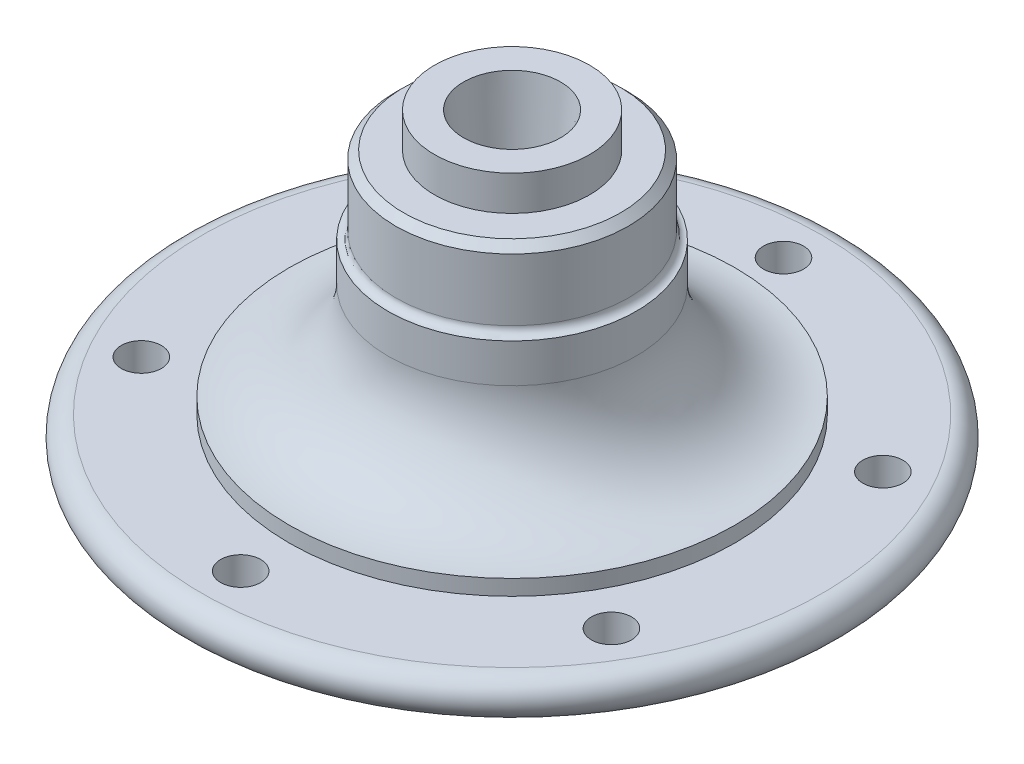
SolidWorks part; units mm, degrees
ref_plane "Front Plane" through (0, 0, 0) normal (0, 0, 1) x (1, 0, 0)
ref_plane "Top Plane" through (0, 0, 0) normal (0, 1, 0) x (1, 0, 0)
ref_plane "Right Plane" through (0, 0, 0) normal (1, 0, 0) x (0, 0, -1)
sketch "Croquis1" plane through (0, 0, 0) normal (0, 0, 1) x (1, 0, 0)
  line L0 (0, 0) -> (0, 90)
  line L1 (0, 90) -> (20, 90)
  line L2 (20, 90) -> (20, 81)
  line L3 (20, 81) -> (28, 81)
  line L4 (30, 79) -> (30, 62.995)
  line L5 (0, 0) -> (40, 0)
  line L6 (40, 0) -> (40, 12)
  line L7 (40, 12) -> (80, 12)
  line L9 (80, 22) -> (57.5, 22)
  line L10 (57.5, 22) -> (57.5, 26)
  line L11 (32, 60.995) -> (32, 50.995)
  line L12 (28, 81) -> (30, 79)
  arc A0 (80, 12) -> (80, 22) centre (80, 17) ccw
  arc A1 (32, 50.995) -> (57.5, 26) centre (57, 50.995) ccw
  arc A2 (32, 60.995) -> (30, 62.995) centre (32, 62.995) cw
  point P7 (30, 81)
  dimension "D5" = 2
  dimension "D4" = 5
  dimension "D11" = 32
  dimension "D14" = 25
  dimension "D2" = 30
  dimension "D1" = 40
  dimension "D3" = 20
  dimension "D6" = 8
  dimension "D7" = 90
  dimension "D8" = 80
  dimension "D9" = 57.5
  dimension "D10" = 10
  dimension "D12" = 4
  dimension "D13" = 12
  dimension "D15" = 2
revolve "Revolución1" add sketch "Croquis1" angle 360 about L0
sketch "Croquis2" plane through (0, 90, 0) normal (0, 1, 0) x (1, 0, 0)
  circle A0 centre (0, 0) radius 12.5
  dimension "D1" = 25
extrude "Cortar-Extruir1" cut sketch "Croquis2" against normal blind 20 draft 5
sketch "Croquis3" plane through (0, 12, 0) normal (0, -1, 0) x (1, 0, 0)
  circle A0 centre (0, 70) radius 5.1649
  dimension "D1" = 70
extrude "Cortar-Extruir2" cut sketch "Croquis3" against normal through all
pattern_circular "MatrizC2" count 6 every 60 about axis through (0, 0, 0) along (0, 1, 0) of "Cortar-Extruir2"
